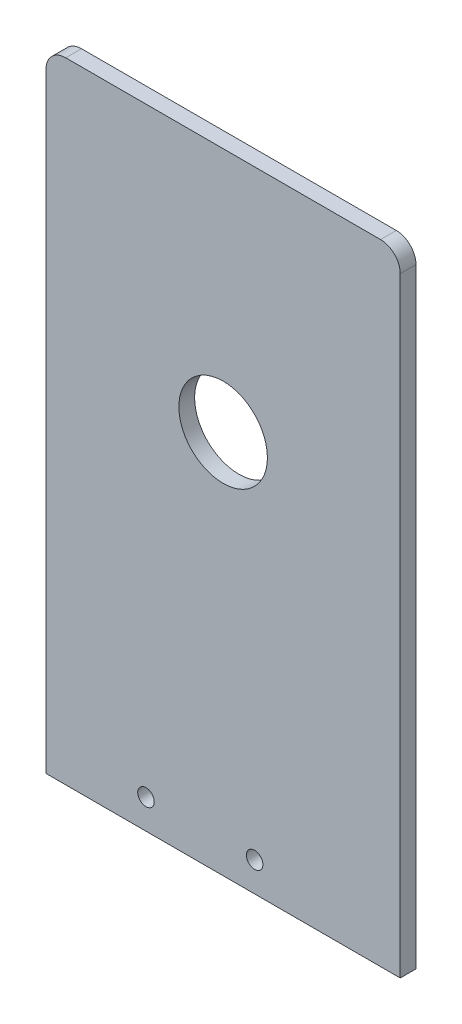
SolidWorks part; units mm, degrees
ref_plane "Front Plane" through (0, 0, 0) normal (0, 0, 1) x (1, 0, 0)
ref_plane "Top Plane" through (0, 0, 0) normal (0, 1, 0) x (1, 0, 0)
ref_plane "Right Plane" through (0, 0, 0) normal (1, 0, 0) x (0, 0, -1)
sketch "Sketch1" plane through (0, 0, 0) normal (0, 0, 1) x (1, 0, 0)
  line L1 (-57.15, -101.6) -> (57.15, -101.6)
  line L2 (-57.15, -101.6) -> (-57.15, 101.6)
  line L3 (-57.15, 101.6) -> (57.15, 101.6)
  line L4 (57.15, -101.6) -> (57.15, 101.6)
  line L5 (-57.15, -101.6) -> (57.15, 101.6) construction
  line L6 (-57.15, 101.6) -> (57.15, -101.6) construction
  point P0 (0, 0)
extrude "Boss-Extrude1" add sketch "Sketch1" along normal blind 5.08
fillet "Fillet1" radius 6.35 2 edges at (-57.15, 101.6, 2.54) (57.15, 101.6, 2.54)
sketch "Sketch3" plane through (0, 0, 5.08) normal (0, 0, 1) x (1, 0, 0)
  line L0 (0, -101.6) -> (0, 22.352)
  line L1 (-57.15, -101.6) -> (57.15, -101.6) construction
  circle A0 centre (0, 22.352) radius 14.2875
extrude "Cut-Extrude1" cut sketch "Sketch3" against normal up to surface (5.08 mm away) up to face at (0, 32.1884, 0)
sketch "Sketch4" plane through (0, 0, 5.08) normal (0, 0, 1) x (1, 0, 0)
  line L0 (57.15, -101.6) -> (57.15, -92.075)
  line L2 (57.15, -101.6) -> (57.15, 95.25) construction
  line L3 (57.15, -92.075) -> (10.16, -92.075)
  circle A6 centre (10.16, -92.075) radius 2.667
  circle A7 centre (-24.892, -92.075) radius 2.667
  dimension "D1" = 9.525
  dimension "D3" = 5.334
  dimension "D2" = 46.99
  dimension "D4" = 2
extrude "Cut-Extrude2" cut sketch "Sketch4" against normal up to surface (5.08 mm away) up to face at (-14.2875, 22.352, 0)
